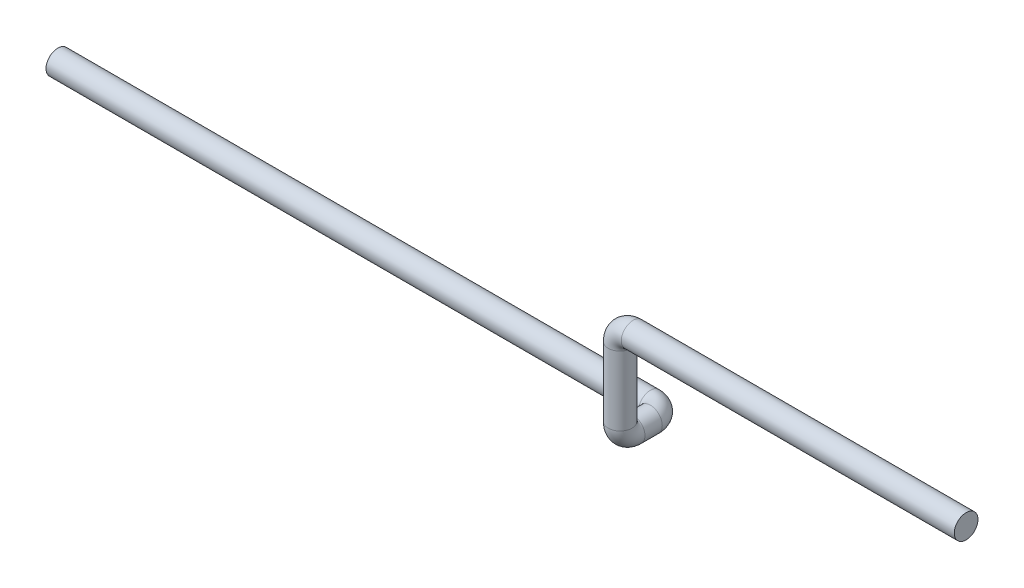
SolidWorks part; units mm, degrees
ref_plane "Alzado" through (0, 0, 0) normal (0, 0, 1) x (1, 0, 0)
ref_plane "Planta" through (0, 0, 0) normal (0, 1, 0) x (1, 0, 0)
ref_plane "Vista lateral" through (0, 0, 0) normal (1, 0, 0) x (0, 0, -1)
sketch3d "Croquis3D1"
  line L0 (0, 0, 0) -> (-385, 0, 0)
  line L1 (-400, -15, 0) -> (-400, -95, 0)
  line L2 (-400, -110, -15) -> (-400, -110, -35)
  line L3 (-415, -110, -50) -> (-1100, -110, -50)
  arc A0 (-385, 0, 0) -> (-400, -15, 0) centre (-385, -15, 0) ccw
  arc A1 (-400, -95, 0) -> (-400, -110, -15) centre (-400, -95, -15) ccw
  arc A2 (-400, -110, -35) -> (-415, -110, -50) centre (-415, -110, -35) ccw
  point P8 (-400, 0, 0)
  point P9 (-385, -15, 15)
  point P12 (-400, -110, 0)
  point P13 (-385, -95, -15)
  point P16 (-400, -110, -50)
  point P17 (-415, -95, -35)
  dimension "D1" = 400
  dimension "D2" = 110
  dimension "D5" = 15
  dimension "D3" = 50
  dimension "D4" = 700
sketch "Croquis1" plane through (0, 0, 0) normal (1, 0, 0) x (0, 0, -1)
  circle A0 centre (0, 0) radius 13.7
  dimension "D1" = 27.4
sweep "Barrer1" add profiles "Croquis1" path "Croquis3D1"
